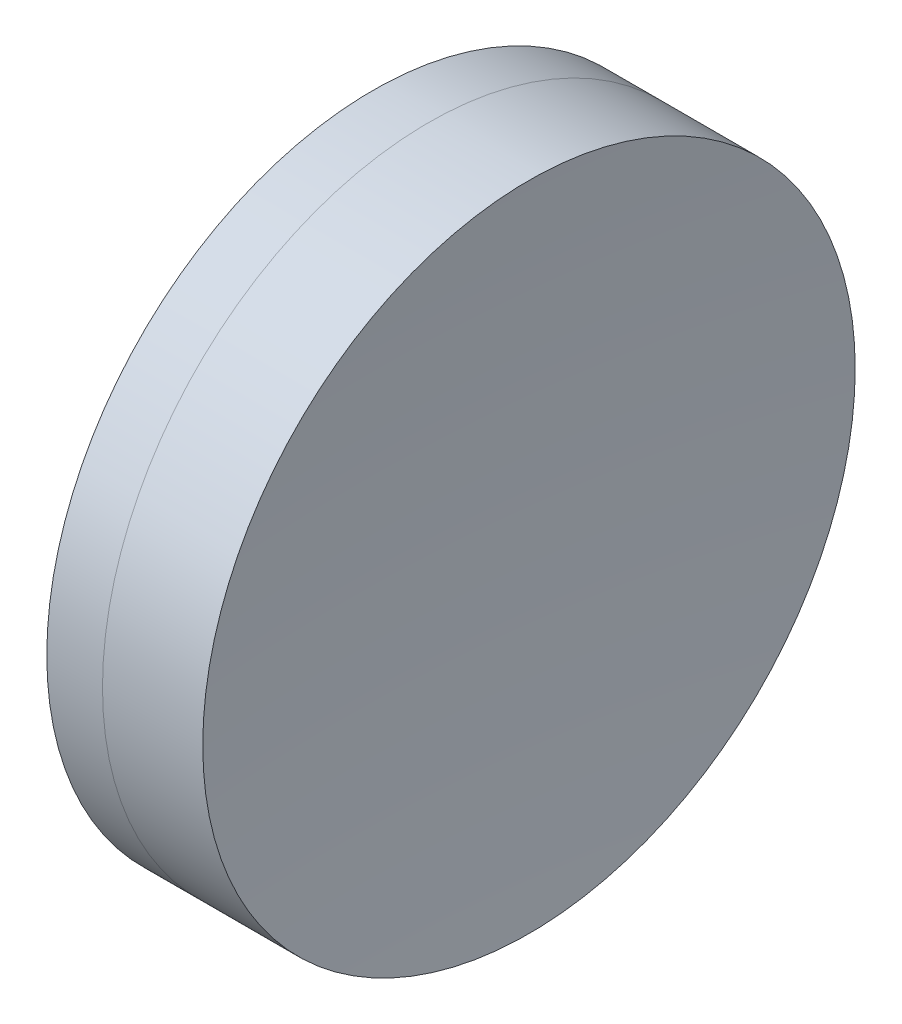
SolidWorks part; units mm, degrees
ref_plane "前视基准面" through (0, 0, 0) normal (0, 0, 1) x (1, 0, 0)
ref_plane "上视基准面" through (0, 0, 0) normal (0, 1, 0) x (1, 0, 0)
ref_plane "右视基准面" through (0, 0, 0) normal (1, 0, 0) x (0, 0, -1)
sketch "草图1" plane through (0, 0, 0) normal (0, 1, 0) x (1, 0, 0)
  line L0 (-0.8161, 0) -> (118.0272, 0) construction
  line L1 (85.4035, -12.7) -> (87.5716, -12.7)
  line L2 (85.4035, 12.7) -> (87.5716, 12.7)
  arc A0 (87.5716, -12.7) -> (87.5716, 12.7) centre (-4.6683, 0) ccw
  arc A1 (85.4035, 12.7) -> (85.4035, -12.7) centre (154.2417, 0) ccw
  point P10 (84.2417, 0)
  point P11 (88.4417, 0)
  dimension "D3" = 70
  dimension "D4" = 93.11
  dimension "D1" = 12.7
  dimension "D2" = 12.7
  dimension "D5" = 4.2
revolve "旋转1" add sketch "草图1" angle 360 about L0
sketch "草图2" plane through (0, 0, 0) normal (0, 1, 0) x (1, 0, 0)
  line L0 (-0.5519, 0) -> (162.8134, 0) construction
  line L2 (87.5716, 12.7) -> (91.4755, 12.7)
  line L3 (87.5716, -12.7) -> (91.4755, -12.7)
  arc A0 (91.4755, 12.7) -> (91.4755, -12.7) centre (242.3017, 0) ccw
  arc A1 (87.5716, -12.7) -> (87.5716, 12.7) centre (-4.6683, 0) ccw construction
  arc A2 (87.5716, -12.7) -> (87.5716, 12.7) centre (-4.6683, 0) ccw
  point P4 (88.4417, 0)
  point P8 (90.9417, 0)
  dimension "D1" = 151.36
  dimension "D2" = 2.5
revolve "旋转2" add sketch "草图2" angle 360 about L0
